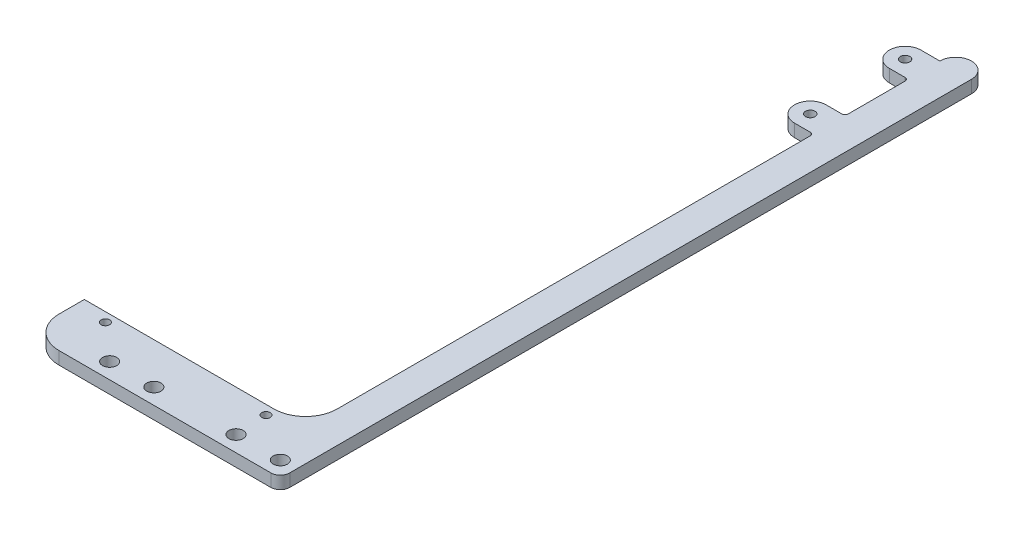
SolidWorks part; units mm, degrees
ref_plane "Front" through (0, 0, 0) normal (0, 0, 1) x (1, 0, 0)
ref_plane "Top" through (0, 0, 0) normal (0, 1, 0) x (1, 0, 0)
ref_plane "Right" through (0, 0, 0) normal (1, 0, 0) x (0, 0, -1)
sketch "Sketch1" plane through (0, 0, 0) normal (0, 1, 0) x (1, 0, 0)
  line L0 (0, 154.95) -> (0, 0)
  line L1 (10, 0) -> (10, 154.95)
  line L2 (0, 0) -> (10, 0)
  line L3 (0, 154.95) -> (10, 154.95) construction
  line L4 (5, 80) -> (68.8779, 80) construction
  arc A0 (0, 154.95) -> (10, 154.95) centre (5, 154.95) cw
  point P6 (25, 146)
  dimension "D1" = 10
  dimension "D4" = 154.95
  dimension "D3" = 20
extrude "Boss-Extrude1" add sketch "Sketch1" along normal blind 4
sketch "Sketch2" plane through (0, 4, 0) normal (0, 1, 0) x (1, 0, 0)
  line L0 (10, 0) -> (40, 0)
  line L1 (40, -10) -> (0, -10) construction
  line L2 (0, -10) -> (0, 0)
  line L3 (40, 0) -> (40, -10) construction
  line L4 (40, -5) -> (0, -5) construction
  line L5 (0, -10) -> (0, -18)
  line L6 (0, -18) -> (54.45, -18)
  line L7 (5, -15.08) -> (49.45, -15.08) construction
  line L8 (45, -10) -> (49.45, -10)
  line L9 (45, -5) -> (45, -10)
  circle A0 centre (5, -15.08) radius 1.35
  circle A1 centre (5, -5) radius 2.25
  circle A2 centre (19, -5) radius 2.25
  circle A3 centre (26, -5) radius 2.25
  circle A4 centre (40, -5) radius 2.25
  circle A5 centre (49.45, -15.08) radius 1.35
  arc A6 (40, 0) -> (45, -5) centre (40, -5) cw
  arc A7 (49.45, -10) -> (54.45, -18) centre (50.222, -15.08) cw
  point P5 (27.225, -15.08)
  point P19 (27.225, -18)
  dimension "D3" = 4.5
  dimension "D4" = 4.5
  dimension "D5" = 4.5
  dimension "D6" = 4.5
  dimension "D13" = 2.7
  dimension "D14" = 2.7
  dimension "D1" = 10
  dimension "D2" = 40
  dimension "D7" = 14
  dimension "D8" = 14
  dimension "D9" = 5
  dimension "D10" = 8
  dimension "D11" = 44.45
  dimension "D12" = 5.08
extrude "Boss-Extrude2" [suppressed] add sketch "Sketch2" against normal blind 4
fillet "Fillet1" [suppressed] radius 3
sketch "Sketch3" plane through (0, 4, 0) normal (0, 1, 0) x (1, 0, 0)
  line L0 (0, -45.7) -> (-70, -45.7)
  line L1 (-60, -63.7) -> (10, -63.7)
  line L2 (10, 0) -> (10, -63.7)
  line L3 (-70, -45.7) -> (-70, -53.7)
  line L4 (-60.4, -48.62) -> (-9.6, -48.62) construction
  line L5 (-49, -58.7) -> (10, -58.7) construction
  line L6 (0, 154.95) -> (0, 0) construction
  line L7 (0, 0.3085) -> (0, -45.7)
  line L8 (0, 0) -> (10, 0) construction
  circle A0 centre (-60.4, -48.62) radius 1.35
  circle A1 centre (-49, -58.7) radius 2.25
  circle A2 centre (-35, -58.7) radius 2.25
  circle A3 centre (-9, -58.7) radius 2.25
  circle A4 centre (5, -58.7) radius 2.25
  circle A5 centre (-9.6, -48.62) radius 1.35
  arc A6 (-70, -53.7) -> (-60, -63.7) centre (-60, -53.7) ccw
  point P2 (-35, -48.62)
  point P8 (-35, -45.7)
  dimension "D3" = 4.5
  dimension "D4" = 4.5
  dimension "D5" = 4.5
  dimension "D14" = 2.7
  dimension "D7" = 14
  dimension "D12" = 5.08
  dimension "D2" = 4.5
  dimension "D15" = 2.7
  dimension "D6" = 14
  dimension "D9" = 49
  dimension "D1" = 18
  dimension "D8" = 45.7
  dimension "D10" = 5
  dimension "D11" = 5
  dimension "D16" = 50.8
  dimension "D17" = 70
  dimension "D18" = 10
extrude "Boss-Extrude3" add sketch "Sketch3" against normal blind 4
fillet "Fillet2" radius 3 1 edges at (10, 2, 63.7)
sketch "Sketch5" [suppressed] plane through (0, 4, 0) normal (0, 1, 0) x (1, 0, 0)
  line L3 (10, 3) -> (10, 148.65) construction
  line L5 (16, 133.65) -> (10, 133.65)
  line L7 (16, 123.65) -> (10, 123.65)
  arc A0 (16, 133.65) -> (16, 123.65) centre (16, 128.65) cw
  circle A1 centre (16, 128.65) radius 1.5
  arc A3 (10, 148.65) -> (0, 148.65) centre (5, 148.65) ccw construction
  line M7 (10, 3) -> (10, 148.65)
  dimension "D1" = 3
  dimension "D2" = 6
  dimension "D4" = 20
  dimension "D3" = 10
extrude "Boss-Extrude4" [suppressed] add sketch "Sketch5" against normal blind 4 contours A0 L5 L7 A1 M7
fillet "Fillet3" [suppressed] radius 1
sketch "Sketch6" plane through (0, 4, 0) normal (0, 1, 0) x (1, 0, 0)
  line L0 (-6, 154.95) -> (0, 154.95)
  line L1 (0, 144.95) -> (-6, 144.95)
  line L2 (-6, 124.95) -> (0, 124.95)
  line L3 (0, 114.95) -> (-6, 114.95)
  line L4 (0, 154.95) -> (0, 0) construction
  line L5 (-3, 144.95) -> (-3, 124.95) construction
  line L9 (-6, 154.95) -> (-6, 144.95) construction
  line L10 (-6, 124.95) -> (-6, 114.95) construction
  arc A0 (-6, 154.95) -> (-6, 144.95) centre (-6, 149.95) ccw
  arc A1 (-6, 124.95) -> (-6, 114.95) centre (-6, 119.95) ccw
  circle A2 centre (-6, 149.95) radius 1.5
  circle A3 centre (-6, 119.95) radius 1.5
  arc A4 (10, 154.95) -> (0, 154.95) centre (5, 154.95) ccw construction
  point P14 (-3, 134.95)
  line M8 (0, 154.95) -> (0, -45.7)
  dimension "D1" = 10
  dimension "D5" = 3
  dimension "D6" = 3
  dimension "D2" = 10
  dimension "D3" = 30
  dimension "D4" = 6
  dimension "D7" = 20
extrude "Boss-Extrude5" add sketch "Sketch6" against normal blind 4 contours L0 A0 L1 A2 M8 | L2 A1 L3 A3 M8
fillet "Fillet4" radius 1 3 edges at (0, 2, -114.95) (0, 2, -124.95) (0, 2, -144.95)
sketch "Sketch7" [suppressed] plane through (0, 4, 0) normal (0, 1, 0) x (1, 0, 0)
  line L1 (0, 148.65) -> (-16, 148.65)
  line L2 (0, 148.65) -> (0, 122.65)
  line L3 (0, 122.65) -> (-16, 122.65)
  line L4 (-16, 148.65) -> (-16, 122.65)
  point P8 (-16, 135.65)
  dimension "D1" = 16
  dimension "D3" = 26
extrude "Boss-Extrude6" [suppressed] add sketch "Sketch7" against normal blind 4
sketch "Sketch8" [suppressed] plane through (0, 4, 0) normal (0, 1, 0) x (1, 0, 0)
  line L0 (-16, 148.65) -> (-16, 122.65) construction
  line L1 (-16, 135.65) -> (10, 135.65) construction
  line L3 (10, 134.65) -> (10, 148.65) construction
  circle A0 centre (-3, 135.65) radius 8
  point P4 (-16, 135.65)
  dimension "D1" = 16
extrude "Cut-Extrude1" [suppressed] cut sketch "Sketch8" against normal blind 4
fillet "Fillet5" radius 10 1 edges at (0, 2, 45.7)
equation "\"D4@Sketch2\"=\"D3@Sketch2\""
equation "\"D5@Sketch2\"=\"D3@Sketch2\""
equation "\"D6@Sketch2\"=\"D3@Sketch2\""
equation "\"D9@Sketch2\"=(\"D1@Sketch2\"-\"D6@Sketch2\")/2+(\"D6@Sketch2\"/2)"
equation "\"D5@Sketch3\"=\"D2@Sketch3\""
equation "\"D4@Sketch3\"=\"D2@Sketch3\""
equation "\"D3@Sketch3\"=\"D2@Sketch3\""
equation "\"D7@Sketch3\"=\"D6@Sketch3\""
equation "\"D2@Sketch6\"=\"D1@Sketch6\""
equation "\"D6@Sketch6\"=\"D5@Sketch6\""
equation "\"D18@Sketch3\"=\"D11@Sketch3\"*2"
equation "\"D15@Sketch3\"=\"D14@Sketch3\""
equation "\"D14@Sketch2\"=\"D13@Sketch2\""
